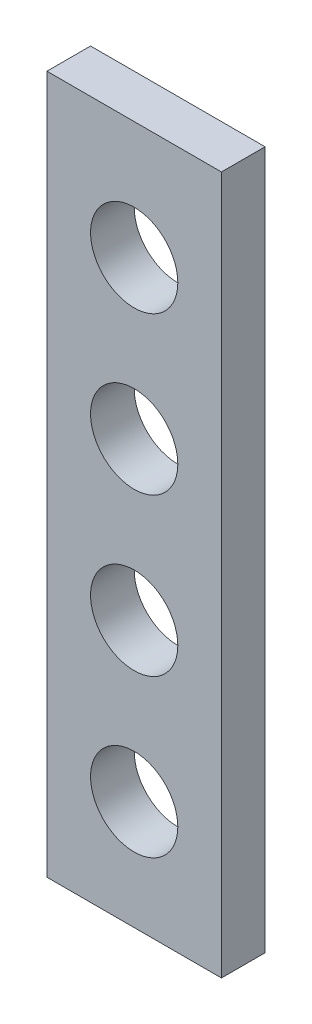
SolidWorks part; units mm, degrees
ref_plane "Front Plane" through (0, 0, 0) normal (0, 0, 1) x (1, 0, 0)
ref_plane "Top Plane" through (0, 0, 0) normal (0, 1, 0) x (1, 0, 0)
ref_plane "Right Plane" through (0, 0, 0) normal (1, 0, 0) x (0, 0, -1)
sketch "Sketch1" plane through (0, 0, 0) normal (0, 0, 1) x (1, 0, 0)
  line L1 (-148.2944, 50.1168) -> (-108.2944, 50.1168)
  line L2 (-148.2944, 50.1168) -> (-148.2944, 210.1168)
  line L3 (-148.2944, 210.1168) -> (-108.2944, 210.1168)
  line L4 (-108.2944, 50.1168) -> (-108.2944, 210.1168)
  dimension "D1" = 160
  dimension "D2" = 40
extrude "Boss-Extrude1" add sketch "Sketch1" along normal blind 10
sketch "Sketch2" plane through (0, 0, 10) normal (0, 0, 1) x (1, 0, 0)
  line L0 (-108.2944, 50.1168) -> (-108.2944, 210.1168) construction
  line L1 (-148.2944, 50.1168) -> (-108.2944, 50.1168) construction
  circle A0 centre (-128.2944, 75.1168) radius 10
  dimension "D1" = 20
  dimension "D2" = 20
  dimension "D3" = 25
extrude "Cut-Extrude1" cut sketch "Sketch2" against normal through all
sketch "Sketch3" plane through (0, 0, 0) normal (0, 0, 1) x (1, 0, 0)
  line L0 (-128.2944, 50.1168) -> (-128.2944, 167.986) construction
  line L1 (-148.2944, 50.1168) -> (-108.2944, 50.1168) construction
pattern_linear "LPattern1" count 4 spacing 36 along (0, 1, 0) of "Cut-Extrude1"
